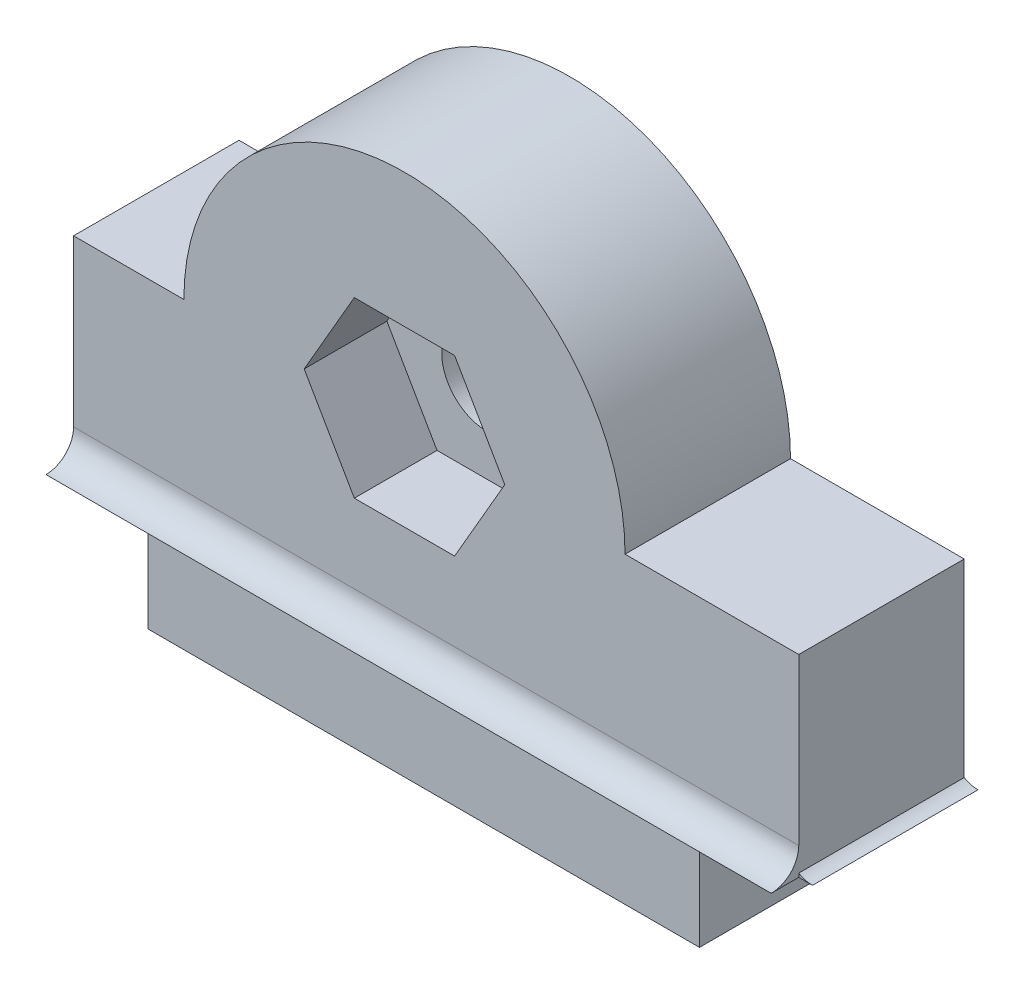
SolidWorks part; units mm, degrees
ref_plane "Front Plane" through (0, 0, 0) normal (0, 0, 1) x (1, 0, 0)
ref_plane "Top Plane" through (0, 0, 0) normal (0, 1, 0) x (1, 0, 0)
ref_plane "Right Plane" through (0, 0, 0) normal (1, 0, 0) x (0, 0, -1)
sketch "Sketch1" plane through (0, 0, 0) normal (0, 0, 1) x (1, 0, 0)
  line L0 (0, 0) -> (20, 0)
  line L1 (0, 0) -> (0, 4)
  line L2 (20, 0) -> (20, 4)
  line L3 (0, 4) -> (-2.7, 4)
  line L4 (23.6, 11) -> (23.6, 4)
  line L5 (-2.7, 4) -> (-2.7, 11)
  line L6 (-2.7, 11) -> (1.3, 11)
  line L7 (17.3, 11) -> (23.6, 11)
  line L8 (23.6, 4) -> (20, 4)
  line L11 (11.1187, 14.15) -> (7.4813, 14.15)
  line L12 (7.4813, 14.15) -> (5.6627, 11)
  line L13 (5.6627, 11) -> (7.4813, 7.85)
  line L14 (7.4813, 7.85) -> (11.1187, 7.85)
  line L15 (11.1187, 7.85) -> (12.9373, 11)
  line L16 (12.9373, 11) -> (11.1187, 14.15)
  arc A0 (17.3, 11) -> (1.3, 11) centre (9.3, 11) ccw
  circle A1 centre (9.3, 11) radius 3.15 construction
  point P19 (10, 0)
  dimension "D5" = 23.6
  dimension "D6" = 20
  dimension "D2" = 7
  dimension "D4" = 6.3
  dimension "D7" = 2.7
  dimension "D9" = 4
extrude "Boss-Extrude1" add sketch "Sketch1" along normal blind 6
sketch "Sketch2" plane through (-2.7, 0, 0) normal (-1, 0, 0) x (0, 0, 1)
  line L0 (3, 0) -> (3, 7) construction
  line L1 (6, 4) -> (6, 5)
  line L2 (6, 4) -> (7, 4)
  line L3 (0, 4) -> (-1, 4) construction
  line L4 (0, 4) -> (0, 5) construction
  arc A0 (6, 5) -> (7, 4) centre (7, 5) ccw
  arc A1 (0, 5) -> (-1, 4) centre (-1, 5) cw construction
  dimension "D1" = 1
  dimension "D2" = 1
  dimension "D3" = 6
  dimension "D4" = 3
  dimension "D5" = 4
extrude "Boss-Extrude2" add sketch "Sketch2" against normal up to surface (26.3 mm away) up to face at (23.6, 7.5, 3)
sketch "Sketch4" plane through (0, 0, 6) normal (0, 0, 1) x (1, 0, 0)
  line L0 (10.8, 0) -> (10.8, 7) construction
  line L1 (23.1, 4) -> (23.1, 5)
  line L2 (23.1, 4) -> (24.1, 4)
  line L3 (-1.5, 4) -> (-2.5, 4)
  line L4 (-1.5, 4) -> (-1.5, 5)
  arc A0 (23.1, 5) -> (24.1, 4) centre (24.1, 5) ccw
  arc A1 (-1.5, 5) -> (-2.5, 4) centre (-2.5, 5) cw
  dimension "D1" = 1
  dimension "D2" = 1
  dimension "D3" = 10.8
  dimension "D4" = 12.3
  dimension "D5" = 4
extrude "Boss-Extrude3" add sketch "Sketch4" against normal up to surface (6 mm away) up to face at (10.04, 6.8, 0)
sketch "Sketch8" plane through (0, 0, 0) normal (0, 0, 1) x (1, 0, 0)
  line L0 (5.6627, 11) -> (12.9373, 11) construction
  line L1 (11.1187, 14.15) -> (7.4813, 14.15) construction
  line L4 (7.4813, 14.15) -> (5.6627, 11)
  line L5 (5.6627, 11) -> (7.4813, 7.85)
  line L6 (7.4813, 7.85) -> (11.1187, 7.85)
  line L7 (11.1187, 7.85) -> (12.9373, 11)
  line L8 (12.9373, 11) -> (11.1187, 14.15)
  line L9 (11.1187, 14.15) -> (7.4813, 14.15)
  circle A0 centre (9.3, 11) radius 3.15 construction
  circle A1 centre (9.3, 11) radius 1.65
  point P4 (9.3, 11)
  point P6 (9.3, 7.85)
  point P14 (9.3, 14.15)
  dimension "D1" = 6.3
  dimension "D2" = 3.3
extrude "Boss-Extrude4" add sketch "Sketch8" along normal blind 3
equation "\"D4@Sketch1\" = 6 + \"tol1@parametersSketch@prostheticParameters.SLDPRT\""
equation "\"D1@Sketch8\"= 6 + \"tol1@parametersSketch@prostheticParameters.SLDPRT\""
equation "\"D2@Sketch8\"= 3 + \"tol1@parametersSketch@prostheticParameters.SLDPRT\""
